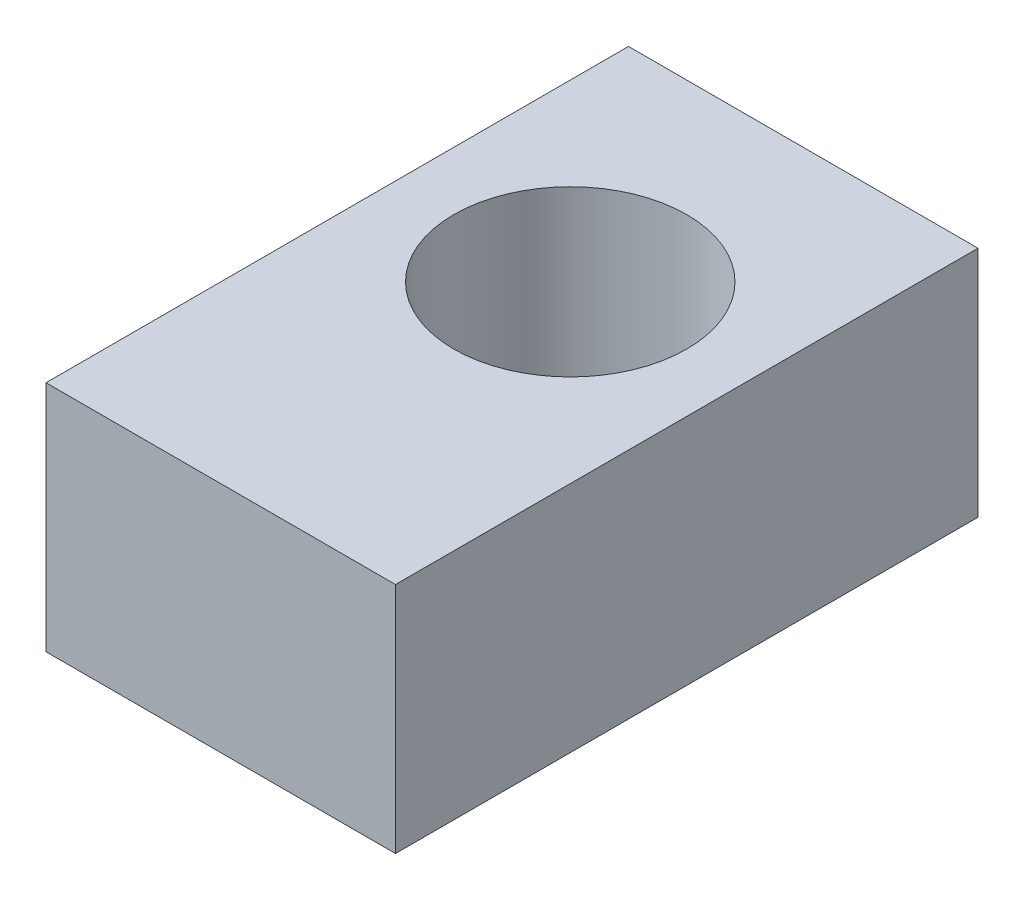
SolidWorks part; units mm, degrees
ref_plane "Front Plane" through (0, 0, 0) normal (0, 0, 1) x (1, 0, 0)
ref_plane "Top Plane" through (0, 0, 0) normal (0, 1, 0) x (1, 0, 0)
ref_plane "Right Plane" through (0, 0, 0) normal (1, 0, 0) x (0, 0, -1)
sketch "Sketch1" plane through (0, 0, 0) normal (0, 1, 0) x (1, 0, 0)
  line L0 (0, 0) -> (0, 50)
  line L1 (0, 50) -> (30, 50)
  line L2 (30, 50) -> (30, 0)
  line L3 (30, 0) -> (0, 0)
  line L4 (15, 30) -> (15, 0) construction
  circle A0 centre (15, 30) radius 10
  dimension "D3" = 20
  dimension "D1" = 50
  dimension "D2" = 30
  dimension "D4" = 30
extrude "Boss-Extrude1" add sketch "Sketch1" along normal mid plane 20
